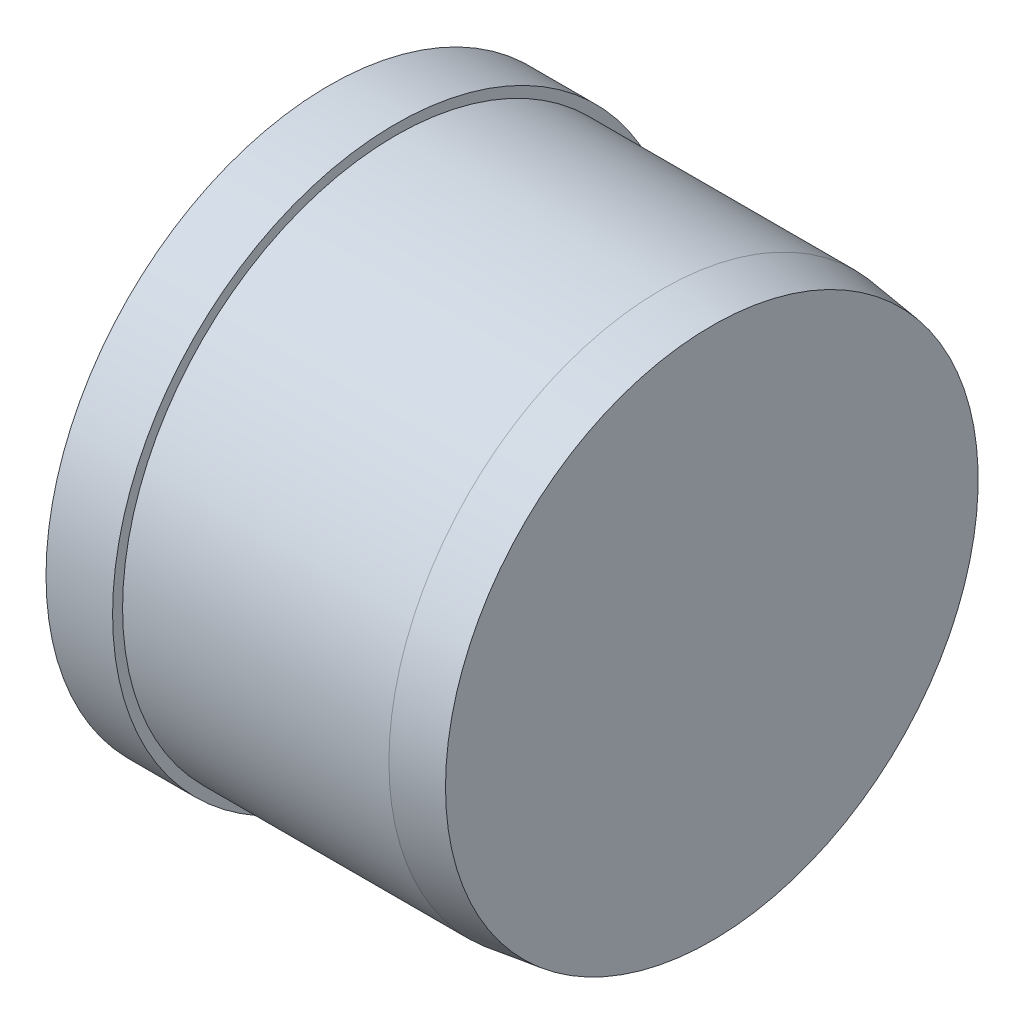
SolidWorks part; units mm, degrees
ref_plane "Front Plane" through (0, 0, 0) normal (0, 0, 1) x (1, 0, 0)
ref_plane "Top Plane" through (0, 0, 0) normal (0, 1, 0) x (1, 0, 0)
ref_plane "Right Plane" through (0, 0, 0) normal (1, 0, 0) x (0, 0, -1)
sketch "Sketch1" plane through (0, 0, 0) normal (0, 0, 1) x (1, 0, 0)
  line L0 (0, 0) -> (57.5, 0) construction
  line L1 (57.5, 0) -> (57.5, 40)
  line L2 (57.5, 40) -> (50, 41)
  line L3 (50, 41) -> (10, 41)
  line L4 (10, 41) -> (10, 42.5)
  line L5 (10, 42.5) -> (0, 42.5)
  line L6 (0, 42.5) -> (0, 0)
  line L7 (0, 0) -> (57.5, 0)
  dimension "D1" = 42.5
  dimension "D2" = 41
  dimension "D3" = 40
  dimension "D4" = 10
  dimension "D5" = 7.5
  dimension "D6" = 40
revolve "Revolve1" add sketch "Sketch1" angle 360 about L0
